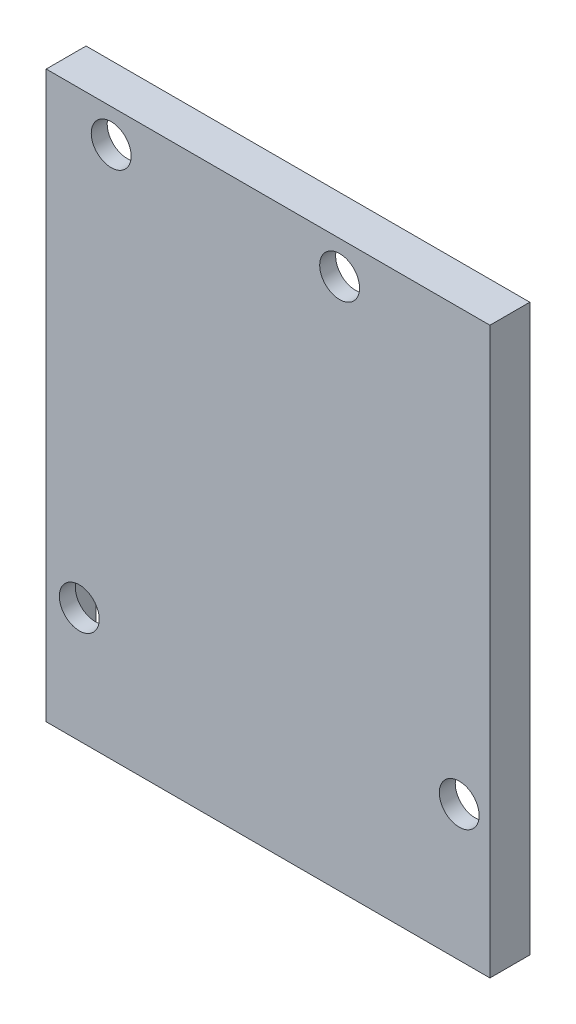
SolidWorks part; units mm, degrees
ref_plane "Front Plane" through (0, 0, 0) normal (0, 0, 1) x (1, 0, 0)
ref_plane "Top Plane" through (0, 0, 0) normal (0, 1, 0) x (1, 0, 0)
ref_plane "Right Plane" through (0, 0, 0) normal (1, 0, 0) x (0, 0, -1)
sketch "Sketch1" plane through (0, 0, 0) normal (0, 0, 1) x (1, 0, 0)
  line L1 (27.825, -35.45) -> (-27.825, -35.45)
  line L2 (27.825, -35.45) -> (27.825, 35.45)
  line L3 (27.825, 35.45) -> (-27.825, 35.45)
  line L4 (-27.825, -35.45) -> (-27.825, 35.45)
  line L5 (27.825, -35.45) -> (-27.825, 35.45) construction
  line L6 (27.825, 35.45) -> (-27.825, -35.45) construction
  point P0 (0, 0)
  dimension "D1" = 70.9
  dimension "D2" = 55.65
extrude "Boss-Extrude1" add sketch "Sketch1" along normal blind 5
sketch "Sketch2" plane through (0, 0, 0) normal (0, 0, -1) x (-1, 0, 0)
  line L0 (23.6765, -20.9918) -> (-23.9735, -20.9918) construction
  line L1 (-23.9735, -20.9918) -> (-23.9735, -18.4918) construction
  line L2 (23.6765, -20.9918) -> (23.6765, 31.3082) construction
  line L3 (23.6765, 31.3082) -> (19.6765, 31.3082) construction
  line L4 (-23.9735, -18.4918) -> (-23.9735, 31.3082) construction
  line L5 (-23.9735, 31.3082) -> (-8.9735, 31.3082) construction
  circle A0 centre (-8.9735, 31.3082) radius 2.5
  circle A1 centre (-23.9735, -18.4918) radius 2.5
  circle A2 centre (23.6765, -20.9918) radius 2.5
  circle A3 centre (19.6765, 31.3082) radius 2.5
  point P8 (0, 0)
  point P9 (0, 0)
  point P12 (19.8342, 26.4734)
  point P13 (0, 0)
  point P15 (20.1676, 29.8069)
  point P16 (0, 0)
  point P17 (0, 0)
  point P18 (23.5011, -22.4732)
  point P19 (0, 0)
  point P20 (19.4453, 31.307)
  point P21 (0, 0)
  point P22 (23.5282, -20.9951)
  point P23 (0, 0)
  point P24 (23.6765, -20.9918)
  dimension "D1" = 5
  dimension "D2" = 47.65
  dimension "D3" = 2.5
  dimension "D4" = 49.8
  dimension "D5" = 15
  dimension "D6" = 4
sketch "Sketch3" plane through (0, 0, 0) normal (0, 0, -1) x (-1, 0, 0)
  line L1 (26.575, -34.2) -> (-26.575, -34.2)
  line L2 (26.575, -34.2) -> (26.575, 34.2)
  line L3 (26.575, 34.2) -> (-26.575, 34.2)
  line L4 (-26.575, -34.2) -> (-26.575, 34.2)
  line L5 (26.575, -34.2) -> (-26.575, 34.2) construction
  line L6 (26.575, 34.2) -> (-26.575, -34.2) construction
  point P0 (0, 0)
  dimension "D1" = 53.15
  dimension "D2" = 68.4
extrude "Cut-Extrude1" cut sketch "Sketch3" against normal blind 3 contours L4 L3 L2 L1
extrude "Cut-Extrude2" cut sketch "Sketch2" against normal through all contours A1 | A2 | A3 | A0
